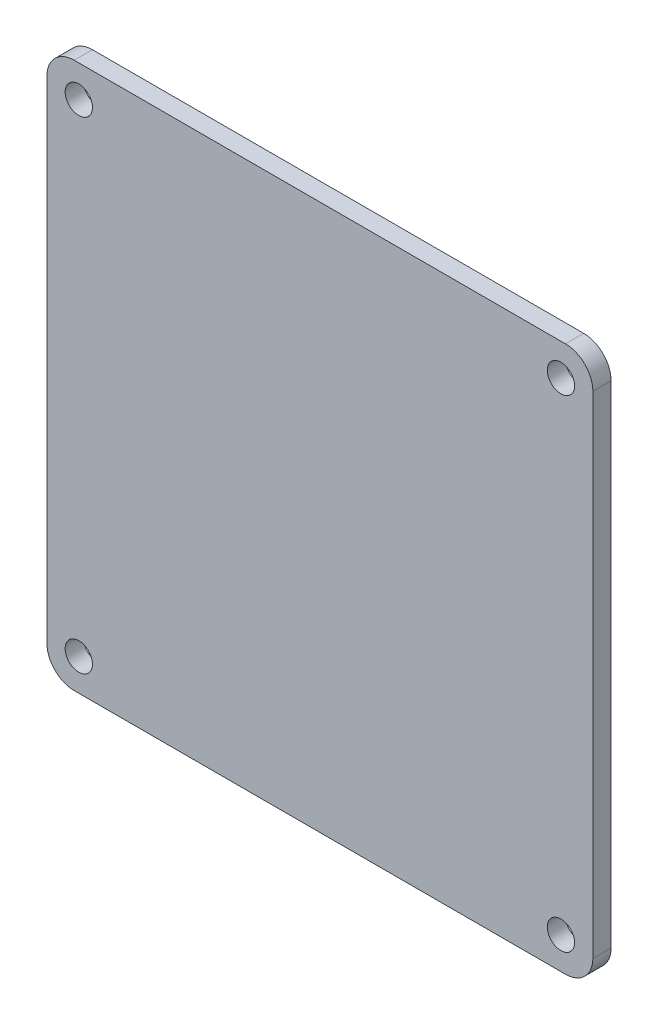
SolidWorks part; units mm, degrees
ref_plane "Front Plane" through (0, 0, 0) normal (0, 0, 1) x (1, 0, 0)
ref_plane "Top Plane" through (0, 0, 0) normal (0, 1, 0) x (1, 0, 0)
ref_plane "Right Plane" through (0, 0, 0) normal (1, 0, 0) x (0, 0, -1)
sketch "Sketch1" plane through (0, 0, 0) normal (0, 0, 1) x (1, 0, 0)
  line L1 (-29.95, 29.95) -> (29.95, 29.95)
  line L2 (-29.95, 29.95) -> (-29.95, -29.95)
  line L3 (-29.95, -29.95) -> (29.95, -29.95)
  line L4 (29.95, 29.95) -> (29.95, -29.95)
  circle A0 centre (-26.45, -26.45) radius 1.5
  circle A1 centre (26.45, -26.45) radius 1.5
  circle A2 centre (-26.45, 26.45) radius 1.5
  circle A3 centre (26.45, 26.45) radius 1.5
  point P0 (0, 0)
extrude "Boss-Extrude1" add sketch "Sketch1" along normal blind 2
fillet "Fillet1" radius 3 4 edges at (29.95, -29.95, 1) (-29.95, -29.95, 1) (29.95, 29.95, 1) (-29.95, 29.95, 1)
